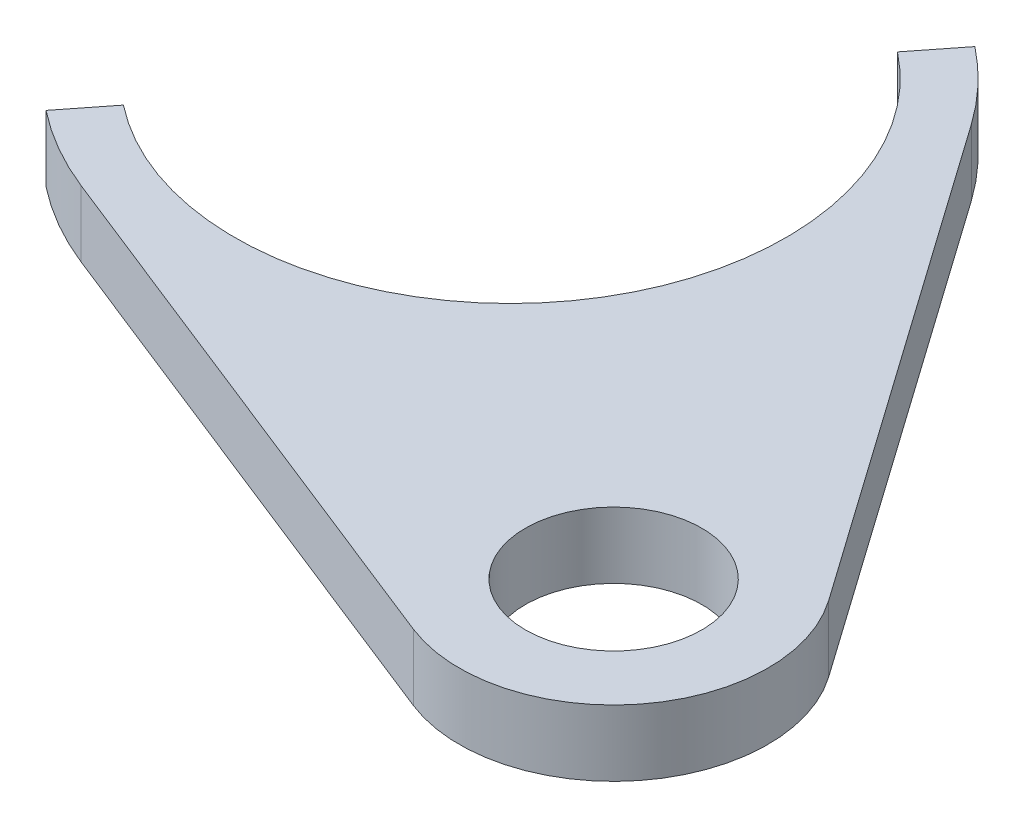
SolidWorks part; units mm, degrees
material "1.0045 (S355JR)"
ref_plane "Płaszczyzna przednia" through (0, 0, 0) normal (0, 0, 1) x (1, 0, 0)
ref_plane "Płaszczyzna górna" through (0, 0, 0) normal (0, 1, 0) x (1, 0, 0)
ref_plane "Płaszczyzna prawa" through (0, 0, 0) normal (1, 0, 0) x (0, 0, -1)
sketch "Szkic1" plane through (0, 0, 0) normal (0, 1, 0) x (1, 0, 0)
  line L0 (-1665.8782, -141.7284) -> (-1690.8247, -131.8455)
  line L1 (-1673.0406, -109.2567) -> (-1657.5789, -131.187)
  line L2 (-1685.3, -117.9) -> (-1663.3, -135.2205) construction
  line L3 (-1694.5788, -129.6857) -> (-1693.0324, -127.7214)
  line L4 (-1677.5676, -108.0786) -> (-1676.0212, -106.1143)
  arc A0 (-1673.0406, -109.2567) -> (-1676.0212, -106.1143) centre (-1685.3, -117.9) ccw
  arc A1 (-1693.0324, -127.7214) -> (-1677.5676, -108.0786) centre (-1685.3, -117.9) ccw
  arc A2 (-1665.8782, -141.7284) -> (-1657.5789, -131.187) centre (-1663.3, -135.2205) ccw
  circle A3 centre (-1663.3, -135.2205) radius 4
  arc A4 (-1694.5788, -129.6857) -> (-1690.8247, -131.8455) centre (-1685.3, -117.9) ccw
  dimension "D1" = 8
  dimension "D2" = 14
  dimension "D3" = 30
  dimension "D4" = 25
  dimension "D5" = 28
  dimension "D6" = 22
  dimension "D7" = 1685.3
  dimension "D8" = 117.9
extrude "Dodanie-wyciągnięcie1" add sketch "Szkic1" along normal blind 3
